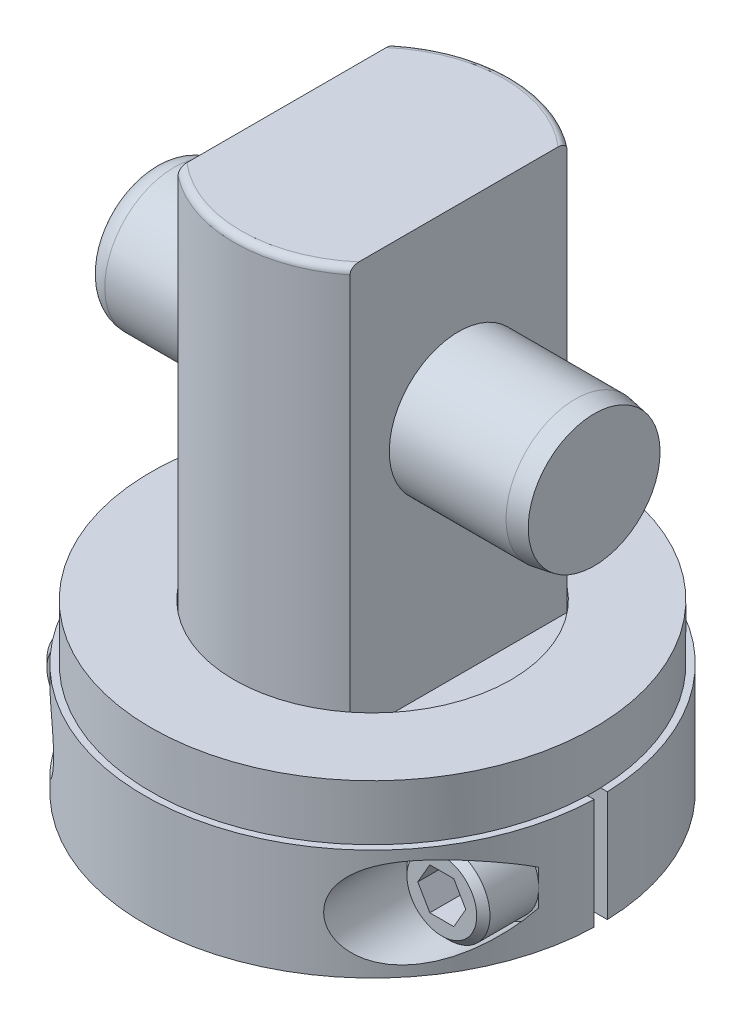
SolidWorks part; units mm, degrees
material "Alloy Steel"
ref_plane "Front Plane" through (0, 0, 0) normal (0, 0, 1) x (1, 0, 0)
ref_plane "Top Plane" through (0, 0, 0) normal (0, 1, 0) x (1, 0, 0)
ref_plane "Right Plane" through (0, 0, 0) normal (1, 0, 0) x (0, 0, -1)
sketch "Sketch1" plane through (0, 0, 0) normal (1, 0, 0) x (0, 0, -1)
  line L0 (0, 56.896) -> (15.875, 56.896)
  line L1 (15.875, 56.896) -> (15.875, 0)
  line L2 (15.875, 0) -> (7.9375, 0)
  line L3 (7.9375, 0) -> (7.9375, -16.129)
  line L4 (7.9375, -16.129) -> (0, -16.129)
  line L5 (0, -16.129) -> (0, 56.896)
  line L6 (0, -15.3594) -> (0, 43.147) construction
  dimension "D1" = 73.025
  dimension "D2" = 16.129
  dimension "D3" = 15.875
  dimension "D4" = 31.75
revolve "Revolve1" add sketch "Sketch1" angle 360 about L6
fillet "Fillet1" radius 0.7874 1 edges at (0, 56.896, -15.875)
sketch "Sketch2" plane through (0, 0, 0) normal (0, 0, 1) x (1, 0, 0)
  line L0 (9.8552, 56.896) -> (15.875, 56.896)
  line L1 (15.875, 56.896) -> (15.875, 10.16)
  line L2 (15.875, 10.16) -> (9.8552, 10.16)
  line L3 (9.8552, 10.16) -> (9.8552, 56.896)
  line L4 (-15.875, 56.896) -> (-9.8552, 56.896)
  line L5 (-9.8552, 56.896) -> (-9.8552, 10.16)
  line L6 (-9.8552, 10.16) -> (-15.875, 10.16)
  line L7 (-15.875, 10.16) -> (-15.875, 56.896)
  line L8 (0, 5.9766) -> (0, 42.131) construction
  line L9 (15.0876, 56.896) -> (-15.0876, 56.896) construction
  line L10 (15.875, 0) -> (15.875, 56.1086) construction
  line L11 (-15.875, 56.1086) -> (-15.875, 0) construction
  dimension "D1" = 19.7104
  dimension "D2" = 46.736
extrude "Cut-Extrude1" cut sketch "Sketch2" against normal through all and the other way through all
sketch "Sketch3" plane through (0, 0, 0) normal (0, -1, 0) x (1, 0, 0)
  circle A0 centre (0, 0) radius 7.0866
  circle A1 centre (0, 0) radius 7.9375 construction
  circle A2 centre (0, 0) radius 7.9375
  dimension "D1" = 14.1732
extrude "Cut-Extrude2" cut sketch "Sketch3" along normal blind 2.54
chamfer "Chamfer1" distance 0.762 angle 45 1 edges at (0, -16.129, -7.9375)
sketch "Sketch4" plane through (0, 0, 0) normal (1, 0, 0) x (0, 0, -1)
  line L0 (-15.875, 0) -> (15.875, 0) construction
  circle A0 centre (0, 36.322) radius 7.94
  dimension "D1" = 15.8801
  dimension "D2" = 36.322
extrude "Extrude1" add sketch "Sketch4" along normal mid plane 50.8
chamfer "Chamfer2" distance 0.381 angle 80 1 edges at (25.4, 36.322, -7.94)
fillet "Fillet2" radius 2.6416 1 edges at (-25.4, 36.322, -7.94)
sketch "Sketch5" plane through (0, 0, 0) normal (0, 1, 0) x (1, 0, 0)
  line L0 (15.8567, 0.762) -> (26.1509, 0.762)
  line L1 (15.8567, -0.762) -> (26.1509, -0.762)
  line L2 (-15.8567, -0.762) -> (-26.1509, -0.762)
  line L3 (-15.8567, 0.762) -> (-26.1509, 0.762)
  line L4 (0, 0) -> (24.3028, 0) construction
  arc A0 (26.1509, 0.762) -> (-26.1509, 0.762) centre (0, 0) ccw
  arc A1 (-26.1509, -0.762) -> (26.1509, -0.762) centre (0, 0) ccw
  arc A2 (15.8567, 0.762) -> (-15.8567, 0.762) centre (0, 0) ccw
  arc A3 (-15.8567, -0.762) -> (15.8567, -0.762) centre (0, 0) ccw
  circle A4 centre (0, 0) radius 15.875 construction
  dimension "D2" = 26.162
  dimension "D1" = 1.524
extrude "Extrude2" add sketch "Sketch5" along normal blind 6.35 and the other way blind 6.35
sketch "Sketch6" plane through (0, 0, 0.762) normal (0, 0, 1) x (1, 0, 0)
  line L0 (0, -5.6718) -> (0, 5.6718) construction
  line L1 (-26.1509, -6.35) -> (26.1509, -6.35) construction
  circle A0 centre (20.6375, 0) radius 5.1562
  circle A1 centre (-20.6375, 0) radius 5.1562
  dimension "D1" = 10.3124
  dimension "D2" = 41.275
  dimension "D3" = 6.35
extrude "Cut-Extrude3" cut sketch "Sketch6" along normal through all from offset 5.588
sketch "Sketch7" plane through (0, 0, 6.35) normal (0, 0, 1) x (1, 0, 0)
  circle A0 centre (20.6375, 0) radius 4.7625
  circle A1 centre (-20.6375, 0) radius 4.7625
  arc A3 (-25.3797, -2.0244) -> (-25.3797, 2.0244) centre (-20.6375, 0) ccw construction
  arc A4 (25.3797, 2.0244) -> (25.3797, -2.0244) centre (20.6375, 0) ccw construction
  dimension "D1" = 9.525
extrude "Extrude3" add sketch "Sketch7" along normal blind 6.35
chamfer "Chamfer3" distance 0.762 angle 45 2 edges at (-15.875, 0, 12.7) (25.4, 0, 12.7)
sketch "Sketch8" plane through (0, 0, 12.7) normal (0, 0, 1) x (1, 0, 0)
  line L0 (0, 0) -> (0, -21.769) construction
  line L1 (22.0123, 2.3813) -> (23.3871, 0)
  line L2 (19.2627, 2.3813) -> (22.0123, 2.3813)
  line L3 (17.8879, 0) -> (19.2627, 2.3813)
  line L4 (19.2627, -2.3812) -> (17.8879, 0)
  line L5 (22.0123, -2.3812) -> (19.2627, -2.3812)
  line L6 (23.3871, 0) -> (22.0123, -2.3812)
  line L8 (-23.3871, 0) -> (-22.0123, -2.3812)
  line L9 (-22.0123, -2.3812) -> (-19.2627, -2.3812)
  line L10 (-19.2627, -2.3812) -> (-17.8879, 0)
  line L11 (-17.8879, 0) -> (-19.2627, 2.3812)
  line L12 (-19.2627, 2.3812) -> (-22.0123, 2.3812)
  line L13 (-22.0123, 2.3812) -> (-23.3871, 0)
  circle A0 centre (-20.6375, 0) radius 2.3813 construction
  circle A1 centre (20.6375, 0) radius 2.3813 construction
  dimension "D2" = 4.7625
extrude "Cut-Extrude4" cut sketch "Sketch8" against normal blind 4.7625
sketch "Sketch10" plane through (0, 0, 0) normal (0, 0, 1) x (1, 0, 0)
  circle A0 centre (20.6375, 0) radius 3.175
  circle A1 centre (-20.6375, 0) radius 3.175
  circle A2 centre (-20.6375, 0) radius 4.7625 construction
  circle A3 centre (20.6375, 0) radius 4.7625 construction
  dimension "D1" = 6.35
extrude "Extrude4" add sketch "Sketch10" along normal up to next and the other way up to next
sketch "Sketch11" plane through (0, 6.35, 0) normal (0, 1, 0) x (-1, 0, 0)
  circle A0 centre (0, 0) radius 25.4
  circle A1 centre (0, 0) radius 15.875
  circle A3 centre (0, 0) radius 7.9375 construction
  dimension "D1" = 50.8
  dimension "D2" = 31.75
extrude "Extrude5" add sketch "Sketch11" along normal blind 6.35
